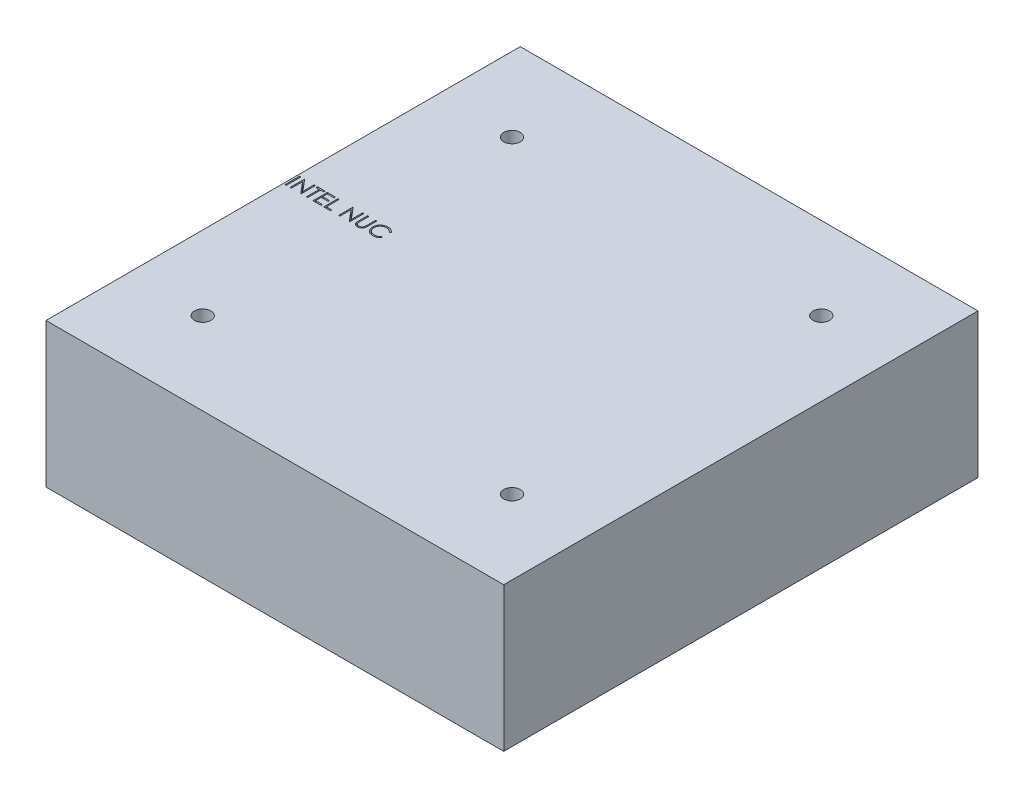
SolidWorks part; units mm, degrees
ref_plane "Front Plane" through (0, 0, 0) normal (0, 0, 1) x (1, 0, 0)
ref_plane "Top Plane" through (0, 0, 0) normal (0, 1, 0) x (1, 0, 0)
ref_plane "Right Plane" through (0, 0, 0) normal (1, 0, 0) x (0, 0, -1)
sketch "Sketch1" plane through (0, 0, 0) normal (0, 1, 0) x (1, 0, 0)
  line L1 (0, 0) -> (111, 0)
  line L2 (0, 0) -> (0, 115)
  line L3 (0, 115) -> (111, 115)
  line L4 (111, 0) -> (111, 115)
  dimension "D1" = 115
  dimension "D2" = 111
extrude "Boss-Extrude1" add sketch "Sketch1" along normal blind 35
sketch "Sketch2" plane through (0, 0, 0) normal (0, -1, 0) x (1, 0, 0)
  line L0 (55.5, 0) -> (55.5, -115) construction
  line L1 (0, 0) -> (111, 0) construction
  line L2 (111, -115) -> (0, -115) construction
  circle A0 centre (18, -20) radius 2
  circle A1 centre (18, -95) radius 2
  circle A2 centre (93, -20) radius 2
  circle A3 centre (93, -95) radius 2
  dimension "D1" = 4
  dimension "D2" = 4
  dimension "D3" = 4
  dimension "D4" = 4
  dimension "D5" = 75
  dimension "D6" = 75
  dimension "D7" = 37.5
  dimension "D8" = 37.5
  dimension "D9" = 37.5
  dimension "D10" = 37.5
  dimension "D11" = 75
  dimension "D12" = 20
extrude "Cut-Extrude1" cut sketch "Sketch2" against normal through all
sketch "Sketch3" plane through (0, 35, 0) normal (0, 1, 0) x (1, 0, 0)
  line L0 (0, 57.5) -> (111, 57.5) construction
  line L1 (0, 115) -> (0, 0) construction
  line L2 (111, 0) -> (111, 115) construction
  text T0 "INTEL NUC"
extrude "Cut-Extrude2" cut sketch "Sketch3" against normal through all
